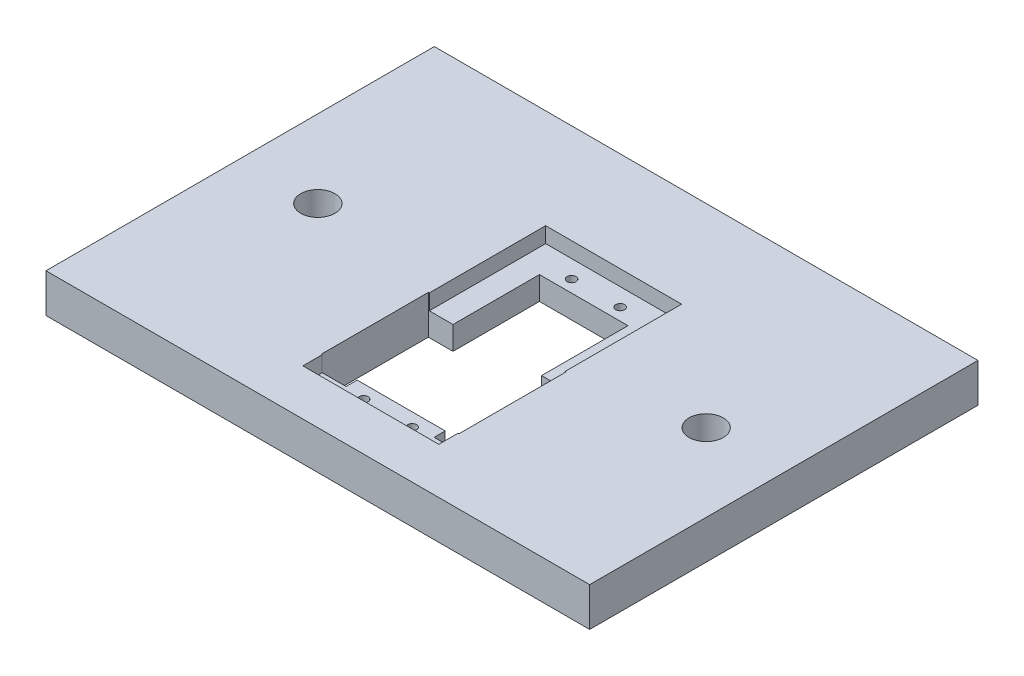
SolidWorks part; units mm, degrees
material "Pine"
ref_plane "Front Plane" through (0, 0, 0) normal (0, 0, 1) x (1, 0, 0)
ref_plane "Top Plane" through (0, 0, 0) normal (0, 1, 0) x (1, 0, 0)
ref_plane "Right Plane" through (0, 0, 0) normal (1, 0, 0) x (0, 0, -1)
sketch "Sketch1" plane through (0, 0, 0) normal (0, 1, 0) x (1, 0, 0)
  line L0 (-88.9, 0) -> (88.9, 0) construction
  line L1 (-88.9, 63.5) -> (88.9, 63.5)
  line L2 (-88.9, 63.5) -> (-88.9, -63.5)
  line L3 (-88.9, -63.5) -> (88.9, -63.5)
  line L4 (88.9, 63.5) -> (88.9, -63.5)
  line L5 (-88.9, 63.5) -> (88.9, -63.5) construction
  line L6 (-88.9, -63.5) -> (88.9, 63.5) construction
  line L22 (2.2699, -24.6155) -> (-29.4884, -24.6155) construction
  line L23 (-29.4884, -24.6155) -> (-16.0181, -38.0859) construction
  line L37 (-29.4884, -24.6155) -> (-16.0181, -11.1451) construction
  line L38 (2.2699, -48.428) -> (2.2699, -24.6155) construction
  line L39 (-12.2081, -38.5062) -> (16.7479, -38.5062)
  line L40 (-12.2081, -38.5062) -> (-12.2081, 21.1838)
  line L41 (-12.2081, 21.1838) -> (16.7479, 21.1838)
  line L42 (16.7479, -38.5062) -> (16.7479, 21.1838)
  circle A0 centre (-63.5, 0) radius 5.588
  circle A1 centre (63.5, 0) radius 5.588
  circle A6 centre (-5.6676, -42.8718) radius 1.4605
  circle A7 centre (10.2074, -42.8718) radius 1.4605
  circle A8 centre (-5.6676, 25.1494) radius 1.4605
  circle A9 centre (10.2074, 25.1494) radius 1.4605
  point P0 (0, 0)
  point P12 (0, 0)
  point P21 (-5.6676, -42.8718)
  point P22 (2.2699, -24.6155)
  point P25 (10.2074, -42.8718)
  point P26 (-5.6676, 25.1494)
  point P27 (10.2074, 25.1494)
  point P47 (20.5579, -38.0859)
  point P48 (20.5579, -11.1451)
  dimension "D4" = 11.176
  dimension "D17" = 3.81
  dimension "D1" = 177.8
  dimension "D2" = 127
  dimension "D3" = 63.5
  dimension "D5" = 63.5
  dimension "D6" = 59.69
  dimension "D7" = 3.9656
  dimension "D8" = 3.9656
  dimension "D9" = 4.3656
  dimension "D10" = 4.3656
  dimension "D11" = 19.05
  dimension "D12" = 90
  dimension "D13" = 28.956
  dimension "D14" = 14.478
  dimension "D15" = 3.81
  dimension "D16" = 13.8906
  dimension "D19" = 15.875
  dimension "D20" = 15.875
  dimension "D21" = 7.9375
extrude "Boss-Extrude1" add sketch "Sketch1" along normal blind 12.7
sketch "Sketch2" plane through (0, 12.7, 0) normal (0, 1, 0) x (1, 0, 0)
  line L0 (-12.2081, -38.5062) -> (16.7479, -38.5062) construction
  line L1 (-19.9551, 30.9628) -> (24.4949, 30.9628)
  line L2 (-19.9551, 30.9628) -> (-19.9551, -48.4376)
  line L3 (-19.9551, -48.4376) -> (24.4949, -48.4376)
  line L4 (24.4949, 30.9628) -> (24.4949, -48.4376)
  line L5 (-19.9551, 30.9628) -> (24.4949, -48.4376) construction
  line L6 (-19.9551, -48.4376) -> (24.4949, 30.9628) construction
  line L7 (2.2699, -48.4376) -> (2.2699, -38.5062) construction
  line L8 (-19.9551, -8.7374) -> (-12.2081, -8.7374) construction
  line L9 (-12.2081, 21.1838) -> (-12.2081, -38.5062) construction
  point P0 (2.2699, -8.7374)
  dimension "D1" = 44.45
  dimension "D2" = 79.4004
  dimension "D3" = 9.9314
  dimension "D4" = 7.747
sketch "Sketch3" plane through (0, 0, 0) normal (0, 1, 0) x (1, 0, 0)
  line L0 (-20.2551, -24.6155) -> (24.795, -24.6155) construction
  line L1 (-20.2551, -7.0895) -> (-12.1271, -7.0895)
  line L2 (-20.2551, -7.0895) -> (-20.2551, -42.1415)
  line L3 (-20.2551, -42.1415) -> (-12.1271, -42.1415)
  line L4 (-12.1271, -7.0895) -> (-12.1271, -42.1415)
  line L5 (-20.2551, -7.0895) -> (-12.1271, -42.1415) construction
  line L6 (-20.2551, -42.1415) -> (-12.1271, -7.0895) construction
  line L7 (16.667, -7.0895) -> (24.795, -7.0895)
  line L8 (16.667, -7.0895) -> (16.667, -42.1415)
  line L9 (16.667, -42.1415) -> (24.795, -42.1415)
  line L10 (24.795, -7.0895) -> (24.795, -42.1415)
  line L11 (16.667, -7.0895) -> (24.795, -42.1415) construction
  line L12 (16.667, -42.1415) -> (24.795, -7.0895) construction
  point P9 (2.2699, -24.6155)
  dimension "D1" = 8.128
  dimension "D2" = 35.052
  dimension "D3" = 8.128
  dimension "D4" = 35.052
extrude "Cut-Extrude3" cut sketch "Sketch3" along normal through all
extrude "Cut-Extrude4" cut sketch "Sketch2" against normal blind 5.08
